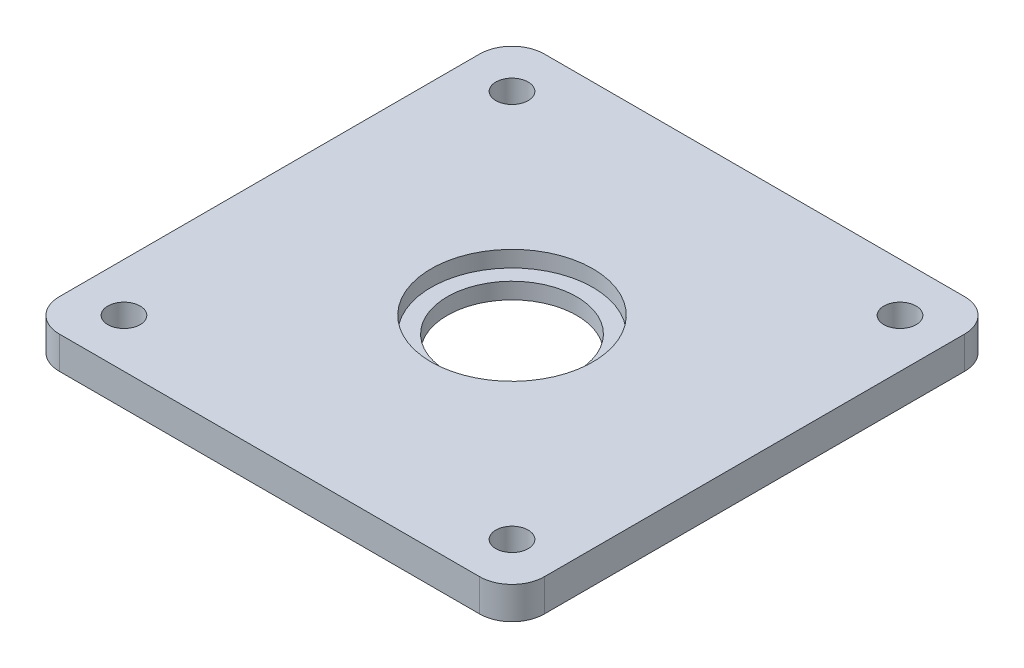
SolidWorks part; units mm, degrees
ref_plane "Front Plane" through (0, 0, 0) normal (0, 0, 1) x (1, 0, 0)
ref_plane "Top Plane" through (0, 0, 0) normal (0, 1, 0) x (1, 0, 0)
ref_plane "Right Plane" through (0, 0, 0) normal (1, 0, 0) x (0, 0, -1)
sketch "Sketch1" plane through (0, 0, 0) normal (0, 1, 0) x (1, 0, 0)
  line L1 (-33.02, -38.1) -> (33.02, -38.1)
  line L2 (-38.1, -33.02) -> (-38.1, 33.02)
  line L3 (-33.02, 38.1) -> (33.02, 38.1)
  line L4 (38.1, -33.02) -> (38.1, 33.02)
  arc A0 (-33.02, -38.1) -> (-38.1, -33.02) centre (-33.02, -33.02) cw
  arc A1 (33.02, -38.1) -> (38.1, -33.02) centre (33.02, -33.02) ccw
  arc A2 (33.02, 38.1) -> (38.1, 33.02) centre (33.02, 33.02) cw
  arc A3 (-38.1, 33.02) -> (-33.02, 38.1) centre (-33.02, 33.02) cw
  circle A4 centre (0, 0) radius 10.16
  circle A8 centre (-30.48, 30.48) radius 2.54
  circle A9 centre (30.48, 30.48) radius 2.54
  circle A10 centre (30.48, -30.48) radius 2.54
  circle A11 centre (-30.48, -30.48) radius 2.54
  point P0 (0, 0)
  dimension "D1" = 5.08
extrude "Boss-Extrude1" add sketch "Sketch1" along normal blind 5.08
sketch "Sketch2" plane through (0, 5.08, 0) normal (0, 1, 0) x (1, 0, 0)
  circle A0 centre (0, 0) radius 12.7
extrude "Cut-Extrude1" cut sketch "Sketch2" against normal blind 2.54
